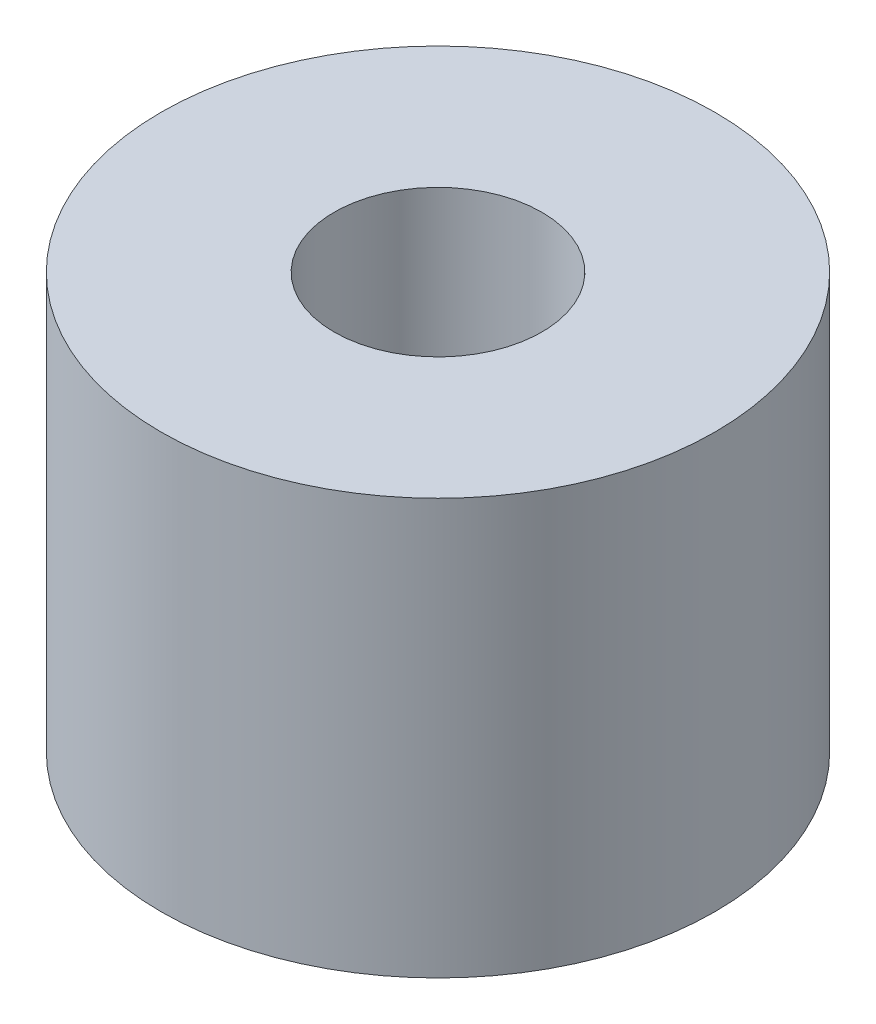
SolidWorks part; units mm, degrees
ref_plane "Front Plane" through (0, 0, 0) normal (0, 0, 1) x (1, 0, 0)
ref_plane "Top Plane" through (0, 0, 0) normal (0, 1, 0) x (1, 0, 0)
ref_plane "Right Plane" through (0, 0, 0) normal (1, 0, 0) x (0, 0, -1)
sketch "Sketch2" plane through (0, 0, 0) normal (0, 1, 0) x (1, 0, 0)
  circle A0 centre (0, 0) radius 4.7625
  circle A1 centre (0, 0) radius 12.7
  dimension "D1" = 9.525
  dimension "D2" = 25.4
extrude "Boss-Extrude1" add sketch "Sketch2" along normal blind 19.05
